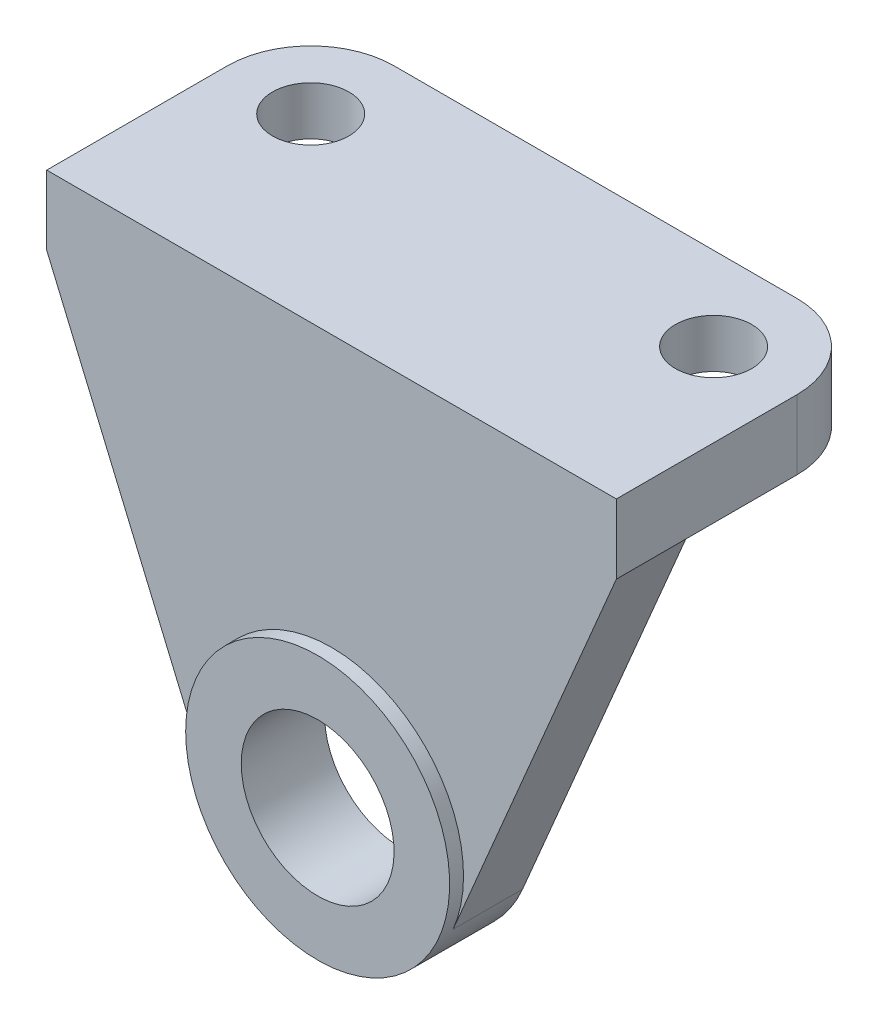
SolidWorks part; units mm, degrees
ref_plane "Alzado" through (0, 0, 0) normal (0, 0, 1) x (1, 0, 0)
ref_plane "Planta" through (0, 0, 0) normal (0, 1, 0) x (1, 0, 0)
ref_plane "Vista lateral" through (0, 0, 0) normal (1, 0, 0) x (0, 0, -1)
sketch "Croquis1" plane through (0, 0, 0) normal (1, 0, 0) x (0, 0, -1)
  line L0 (0, 0) -> (0, 38)
  line L1 (0, 38) -> (2, 38)
  line L2 (2, 38) -> (2, 77)
  line L3 (2, 77) -> (40, 77)
  line L4 (40, 77) -> (40, 67)
  line L5 (40, 67) -> (12, 67)
  line L6 (12, 67) -> (12, 0)
  line L7 (12, 0) -> (0, 0)
  point P8 (36.1165, 1.0194)
  dimension "D1" = 10
  dimension "D2" = 38
  dimension "D3" = 10
  dimension "D4" = 12
  dimension "D5" = 67
  dimension "D6" = 38
extrude "Saliente-Extruir1" add sketch "Croquis1" along normal blind 82
sketch "Croquis2" plane through (0, 0, -12) normal (0, 0, -1) x (-1, 0, 0)
  line L0 (0, 67) -> (-23.5086, 11.5803)
  line L1 (-58.4914, 11.5803) -> (-82, 67)
  line L2 (-41, 67) -> (-41, -3.749) construction
  line L3 (-82, 67) -> (0, 67) construction
  line L4 (-82, 0) -> (0, 0) construction
  line L5 (0, 0) -> (0, 67) construction
  line L6 (-82, 0) -> (-82, 67) construction
  line L7 (0, 0) -> (0, 67)
  line L8 (-82, 0) -> (0, 0)
  line L9 (-82, 0) -> (-82, 67)
  arc A0 (-23.5086, 11.5803) -> (-58.4914, 11.5803) centre (-41, 19) cw
  line M3 (0, 0) -> (0, 67)
  line M5 (-82, 67) -> (-82, 0)
  line M6 (-82, 0) -> (0, 0)
extrude "Cortar-Extruir1" cut sketch "Croquis2" against normal blind 82 contours A0 L1 M6 M5 | L0 A0 L8 M3
sketch "Croquis3" plane through (0, 0, -12) normal (0, 0, -1) x (-1, 0, 0)
  circle A0 centre (-41, 19) radius 11
extrude "Cortar-Extruir2" cut sketch "Croquis3" against normal blind 82
sketch "Croquis5" plane through (0, 0, 0) normal (0, 0, 1) x (1, 0, 0)
  line L0 (69.6984, 38) -> (12.3016, 38) construction
  line L1 (58.4914, 11.5803) -> (69.6984, 38) construction
  line L2 (12.3016, 38) -> (23.5086, 11.5803) construction
  line L3 (58.4914, 11.5803) -> (69.6984, 38)
  line L4 (69.6984, 38) -> (12.3016, 38)
  line L5 (12.3016, 38) -> (23.5086, 11.5803)
  arc A0 (23.5086, 11.5803) -> (58.4914, 11.5803) centre (41, 19) cw
  line M2 (69.6984, 38) -> (12.3016, 38)
  line M3 (12.3016, 38) -> (23.5086, 11.5803)
  line M5 (58.4914, 11.5803) -> (69.6984, 38)
extrude "Cortar-Extruir4" cut sketch "Croquis5" against normal up to surface (2 mm away) contours A0 L4 M3 | A0 M2 M5 up to face at (41, 60.6667, -2)
fillet "Redondeo1" radius 12 1 edges at (0, 72, -40)
fillet "Redondeo2" radius 12 1 edges at (82, 72, -40)
sketch "Croquis7" plane through (0, 67, 0) normal (0, -1, 0) x (1, 0, 0)
  circle A0 centre (12, -28) radius 10
  circle A1 centre (70, -28) radius 10
extrude "Cortar-Extruir6" cut sketch "Croquis7" against normal blind 3
sketch "Croquis8" plane through (0, 67, 0) normal (0, -1, 0) x (1, 0, 0)
  circle A0 centre (12, -28) radius 5.5
  circle A1 centre (70, -28) radius 5.5
extrude "Cortar-Extruir7" cut sketch "Croquis8" against normal through all
